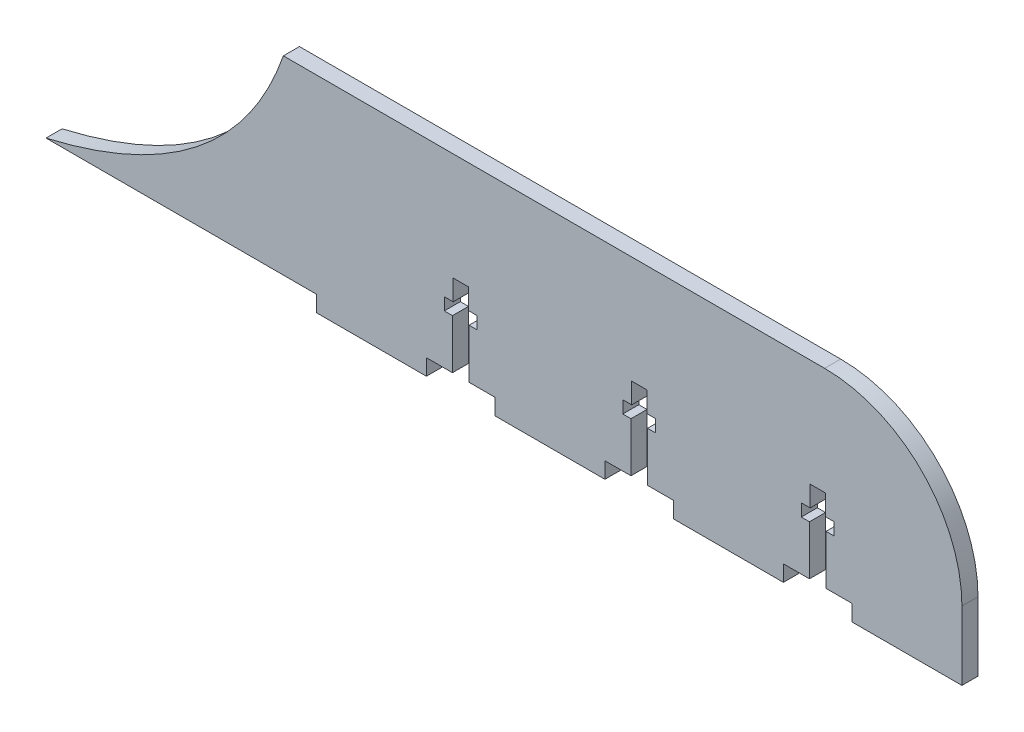
SolidWorks part; units mm, degrees
ref_plane "Front Plane" through (0, 0, 0) normal (0, 0, 1) x (1, 0, 0)
ref_plane "Top Plane" through (0, 0, 0) normal (0, 1, 0) x (1, 0, 0)
ref_plane "Right Plane" through (0, 0, 0) normal (1, 0, 0) x (0, 0, -1)
sketch "Sketch2" plane through (0, 0, 0) normal (0, 0, 1) x (1, 0, 0)
  line L0 (-190.5, 0) -> (0, 0)
  line L1 (0, 0) -> (0, 38.1)
  line L2 (0, 38.1) -> (-125.5187, 38.1)
  line L4 (-125.5187, 38.1) -> (-137.6863, 3.4223) construction
  line L5 (-137.6863, 3.4223) -> (-190.5, 0) construction
  spline S0 degree 2 poles (-125.5187, 38.1) (-137.6863, 3.4223) (-190.5, 0) knots 0 0 0 1 1 1
  dimension "D1" = 38.1
  dimension "D2" = 190.5
extrude "Boss-Extrude2" add sketch "Sketch2" along normal blind 2.9718 contours L0 L1 L2 S0
sketch "Sketch4" plane through (0, 0, 2.9718) normal (0, 0, 1) x (1, 0, 0)
  line L0 (-20.32, 2.9722) -> (-20.32, -12.6967)
  line L1 (-20.32, 2.9722) -> (-33.02, 2.9722)
  line L2 (-33.02, 2.9722) -> (-33.02, -12.6967)
  line L3 (0, 0) -> (0, 38.1) construction
  line L4 (-53.34, 2.9722) -> (-66.04, 2.9722)
  line L5 (-66.04, 2.9722) -> (-66.04, -12.6967)
  line L6 (-53.34, 2.9722) -> (-53.34, -12.6967)
  line L7 (-86.36, 2.9722) -> (-99.06, 2.9722)
  line L8 (-99.06, 2.9722) -> (-99.06, -12.6967)
  line L9 (-86.36, 2.9722) -> (-86.36, -12.6967)
  line L10 (-119.38, 2.9722) -> (-132.08, 2.9722)
  line L11 (-132.08, 2.9722) -> (-194.0698, 2.9722)
  line L12 (-119.38, 2.9722) -> (-119.38, -12.6967)
  line L13 (-132.08, 2.9722) -> (-132.08, -12.6967) [skipped]
  spline M1 degree 2 poles (-125.5187, 38.1) (-137.6863, 3.4223) (-190.5, 0) knots 0 0 0 1 1 1
  line M2 (-190.5, 0) -> (0, 0)
  dimension "D1" = 20.32
  dimension "D2" = 12.7
  dimension "D3" = 4
extrude "Cut-Extrude1" cut sketch "Sketch4" against normal blind 2.9718 contours L12 L10 L11 M1 M2 | L9 L7 L8 M2 | L6 L4 L5 M2 | L1 L2 L0 M2
sketch "Sketch5" plane through (0, 0, 2.9718) normal (0, 0, 1) x (1, 0, 0)
  line L0 (-26.67, 23.7376) -> (-26.67, -7.5916)
  line L1 (-25.273, 18.2122) -> (-28.067, 18.2122)
  line L2 (-25.273, 18.2122) -> (-25.273, 14.4022)
  line L3 (-25.273, 14.4022) -> (-23.622, 14.4022)
  line L4 (-23.622, 14.4022) -> (-23.622, 12.1162)
  line L5 (-23.622, 12.1162) -> (-25.1352, 12.1162)
  line L6 (-25.1352, 12.1162) -> (-25.1352, 2.9722)
  line L7 (-20.32, 2.9722) -> (-33.02, 2.9722) construction
  line L8 (-29.718, 14.4022) -> (-29.718, 12.1162)
  line L9 (-28.067, 14.4022) -> (-29.718, 14.4022)
  line L10 (-29.718, 12.1162) -> (-28.2048, 12.1162)
  line L11 (-28.2048, 12.1162) -> (-28.2048, 2.9722)
  line L12 (-28.067, 18.2122) -> (-28.067, 14.4022)
  line L13 (-58.293, 18.2122) -> (-61.087, 18.2122)
  line L14 (-61.087, 18.2122) -> (-61.087, 14.4022)
  line L15 (-61.087, 14.4022) -> (-62.738, 14.4022)
  line L16 (-62.738, 14.4022) -> (-62.738, 12.1162)
  line L17 (-62.738, 12.1162) -> (-61.2248, 12.1162)
  line L18 (-61.2248, 12.1162) -> (-61.2248, 2.9722)
  line L19 (-58.1552, 12.1162) -> (-58.1552, 2.9722)
  line L20 (-58.293, 18.2122) -> (-58.293, 14.4022)
  line L21 (-58.293, 14.4022) -> (-56.642, 14.4022)
  line L22 (-56.642, 14.4022) -> (-56.642, 12.1162)
  line L23 (-56.642, 12.1162) -> (-58.1552, 12.1162)
  line L24 (-91.313, 18.2122) -> (-94.107, 18.2122)
  line L25 (-94.107, 18.2122) -> (-94.107, 14.4022)
  line L26 (-94.107, 14.4022) -> (-95.758, 14.4022)
  line L27 (-95.758, 14.4022) -> (-95.758, 12.1162)
  line L28 (-95.758, 12.1162) -> (-94.2448, 12.1162)
  line L29 (-94.2448, 12.1162) -> (-94.2448, 2.9722)
  line L30 (-91.1752, 12.1162) -> (-91.1752, 2.9722)
  line L31 (-91.313, 18.2122) -> (-91.313, 14.4022)
  line L32 (-91.313, 14.4022) -> (-89.662, 14.4022)
  line L33 (-89.662, 14.4022) -> (-89.662, 12.1162)
  line L34 (-89.662, 12.1162) -> (-91.1752, 12.1162)
  point P3 (-26.67, 8.073)
  point P6 (-26.67, 18.2122)
  point P20 (-26.67, 18.2122)
  line M13 (-99.06, 2.9722) -> (-86.36, 2.9722)
  line M17 (-66.04, 2.9722) -> (-53.34, 2.9722)
  line M21 (-33.02, 2.9722) -> (-20.32, 2.9722)
  dimension "D1" = 1.397
  dimension "D2" = 2.286
  dimension "D3" = 15.24
  dimension "D4" = 3.81
  dimension "D6" = 3.048
  dimension "D5" = 3
extrude "Cut-Extrude2" cut sketch "Sketch5" against normal blind 2.9718 contours L34 L33 L32 L31 L24 L25 L26 L27 L28 L29 L30 M13 | L23 L22 L21 L20 L13 L14 L15 L16 L17 L18 L19 M17 | L1 L12 L9 L8 L10 L11 L0 M21 | L6 L5 L4 L3 L2 L1 L0 M21
fillet "Fillet1" radius 25.4 1 edges at (0, 38.1, 1.4859)
